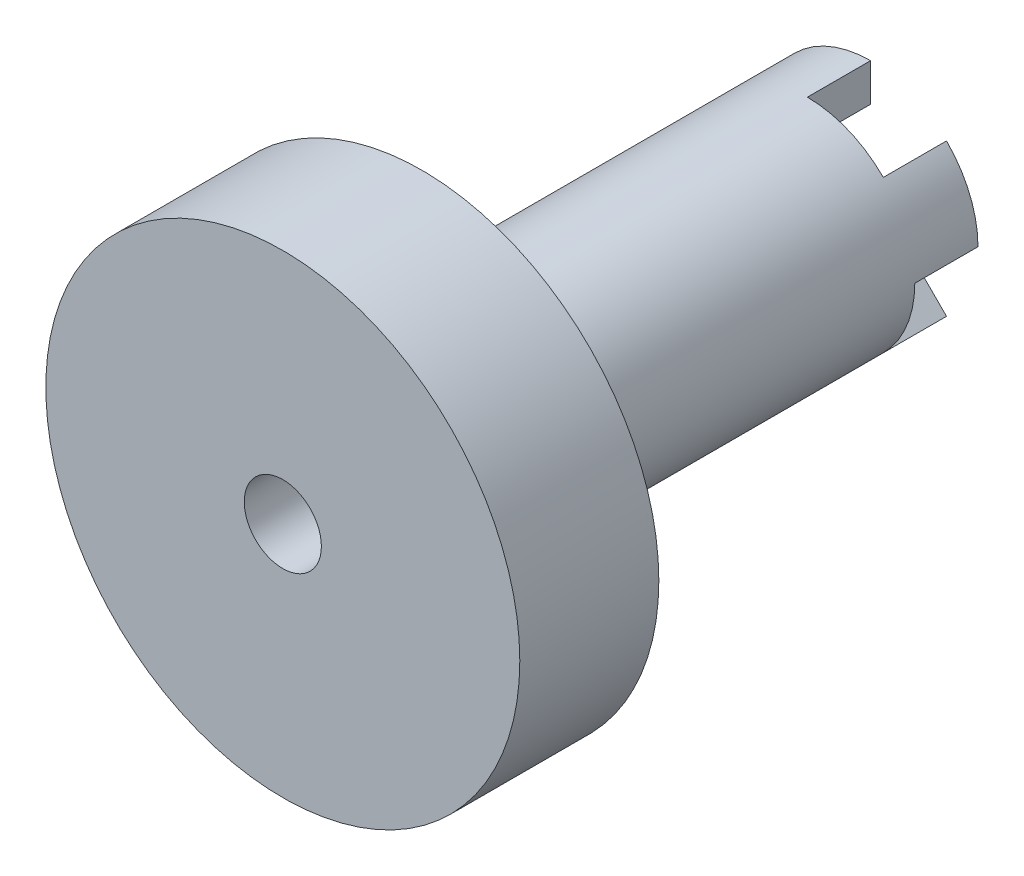
SolidWorks part; units mm, degrees
ref_plane "Front Plane" through (0, 0, 0) normal (0, 0, 1) x (1, 0, 0)
ref_plane "Top Plane" through (0, 0, 0) normal (0, 1, 0) x (1, 0, 0)
ref_plane "Right Plane" through (0, 0, 0) normal (1, 0, 0) x (0, 0, -1)
sketch "Sketch1" plane through (0, 0, 0) normal (0, 0, 1) x (1, 0, 0)
  circle A0 centre (0, 0) radius 4.318
  dimension "D1" = 8.636
extrude "Boss-Extrude1" add sketch "Sketch1" against normal blind 21.082
sketch "Sketch2" plane through (0, 0, 0) normal (0, 0, 1) x (1, 0, 0)
  circle A0 centre (0, 0) radius 9.525
  dimension "D1" = 19.05
extrude "Boss-Extrude2" add sketch "Sketch2" against normal blind 5.588
sketch "Sketch3" plane through (0, 0, -21.082) normal (0, 0, -1) x (-1, 0, 0)
  line L0 (0, -4.318) -> (0, 4.318)
  line L1 (-4.318, 0) -> (4.318, 0)
  line L2 (3.0533, 3.0533) -> (-3.0533, -3.0533)
  line L3 (-3.0533, 3.0533) -> (3.0533, -3.0533)
  circle A0 centre (0, 0) radius 4.318
  circle A1 centre (0, 0) radius 2.8
  point P12 (0, 0)
  point P13 (0, 0)
  circle M5 centre (0, 0) radius 4.318
  dimension "D1" = 8.636
  dimension "D2" = 5.6
  dimension "D3" = 45
  dimension "D4" = 45
extrude "Boss-Extrude3" add sketch "Sketch3" along normal blind 2.54 contours A1 L3 L1 M5 | A1 L2 L0 M5 | A1 L3 L1 M5 | A1 L2 L0 M5
sketch "Sketch6" plane through (0, 0, 0) normal (0, 0, 1) x (1, 0, 0)
  circle A0 centre (0, 0) radius 1.55
  dimension "D1" = 3.1
extrude "Cut-Extrude1" cut sketch "Sketch6" against normal through all
